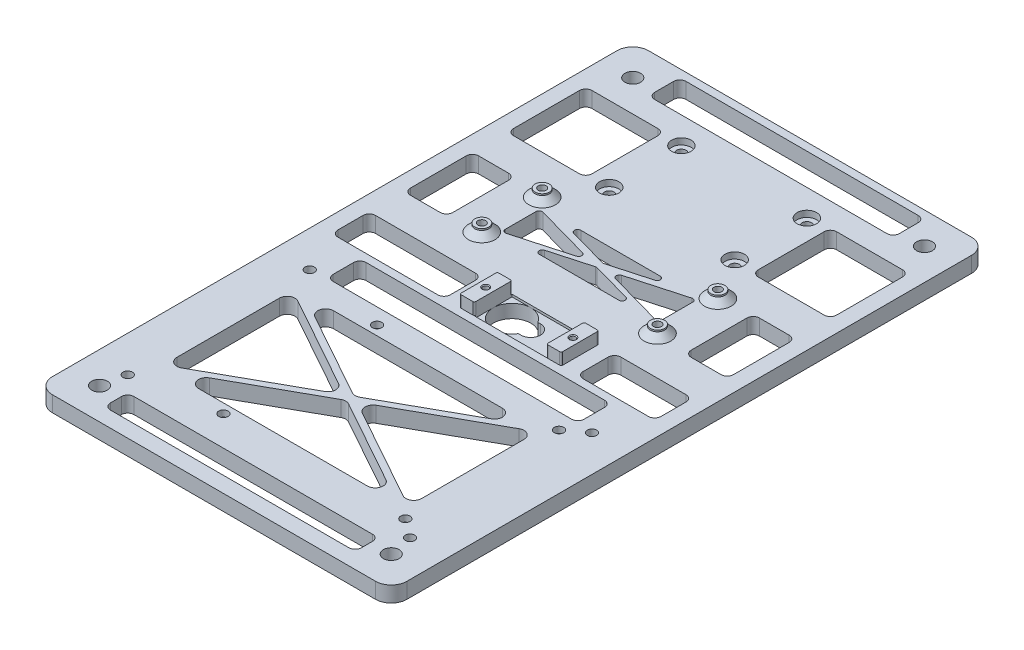
SolidWorks part; units mm, degrees
other "Markup1"
sketch "Sketch25" plane through (-56.5, 8.75, 95) normal (-0.8124, 0.5756, 0.0932) x (-0.5544, -0.812, 0.1827)
ref_plane "Front Plane" through (0, 0, 0) normal (0, 0, 1) x (1, 0, 0)
ref_plane "Top Plane" through (0, 0, 0) normal (0, 1, 0) x (1, 0, 0)
ref_plane "Right Plane" through (0, 0, 0) normal (1, 0, 0) x (0, 0, -1)
sketch "Sketch1" plane through (0, 0, 0) normal (0, 1, 0) x (1, 0, 0)
  line L0 (-56.5, -95) -> (-56.5, 95)
  line L1 (-46.5, -85) -> (46.5, -85) construction
  line L2 (-46.5, -85) -> (-46.5, 85) construction
  line L3 (-46.5, 85) -> (46.5, 85) construction
  line L4 (46.5, -85) -> (46.5, 85) construction
  line L5 (-46.5, -85) -> (46.5, 85) construction
  line L6 (-46.5, 85) -> (46.5, -85) construction
  line L7 (-56.5, 95) -> (56.5, 95)
  line L8 (56.5, -95) -> (56.5, 95)
  line L9 (-56.5, -95) -> (56.5, -95)
  circle A0 centre (46.5, 85) radius 2.5
  circle A1 centre (-46.5, 85) radius 2.5
  circle A2 centre (-46.5, -85) radius 2.5
  circle A3 centre (46.5, -85) radius 2.5
  point P0 (0, 0)
  dimension "D3" = 5
  dimension "D1" = 170
  dimension "D2" = 93
  dimension "D4" = 10
extrude "Boss-Extrude1" add sketch "Sketch1" along normal blind 5
fillet "Fillet1" radius 5 4 edges at (-56.5, 2.5, 95) (-56.5, 2.5, -95) (56.5, 2.5, -95) (56.5, 2.5, 95)
sketch "Sketch2" plane through (0, 5, 0) normal (0, 1, 0) x (1, 0, 0)
  line L0 (-39, -24) -> (-39, -73) construction
  line L1 (-39, -24) -> (39, -24) construction
  line L2 (-39, -20.5) -> (39, -20.5) construction
  line L3 (42.5, -48.5) -> (-39, -48.5) construction
  line L4 (-42.5, -24) -> (-42.5, -73) construction
  line L5 (42.5, -24) -> (42.5, -73) construction
  line L6 (-39, -76.5) -> (39, -76.5) construction
  line L7 (0, -20.5) -> (0, -1.8528) construction
  line L8 (-51.5, -95) -> (51.5, -95) construction
  circle A0 centre (39, -24) radius 1.5
  circle A1 centre (39, -73) radius 1.5
  arc A2 (-39, -20.5) -> (-42.5, -24) centre (-39, -24) ccw construction
  arc A3 (-39, -76.5) -> (-42.5, -73) centre (-39, -73) cw construction
  arc A4 (42.5, -24) -> (39, -20.5) centre (39, -24) ccw construction
  arc A5 (42.5, -73) -> (39, -76.5) centre (39, -73) cw construction
  circle A6 centre (-19, -24) radius 1.5
  circle A7 centre (-19, -73) radius 1.5
  point P14 (1.75, -48.5)
  dimension "D1" = 3
  dimension "D2" = 49
  dimension "D3" = 85
  dimension "D4" = 56
  dimension "D5" = 58
  dimension "D6" = 18.5
extrude "Cut-Extrude1" cut sketch "Sketch2" against normal blind 10
sketch "Sketch3" plane through (0, 5, 0) normal (0, 1, 0) x (1, 0, 0)
  line L0 (-45, -80) -> (45, -80) construction
  line L1 (-47.5, -77.5) -> (-47.5, -19.5) construction
  line L2 (-45, -17) -> (45, -17) construction
  line L3 (47.5, -77.5) -> (47.5, -19.5) construction
  line L4 (-47.5, -80) -> (47.5, -17) construction
  line L5 (-47.5, -17) -> (47.5, -80) construction
  line L6 (-51.5, -95) -> (51.5, -95) construction
  circle A0 centre (45, -19.5) radius 1.5
  circle A1 centre (45, -77.5) radius 1.5
  circle A2 centre (-45, -19.5) radius 1.5
  circle A3 centre (-45, -77.5) radius 1.5
  arc A4 (-47.5, -19.5) -> (-45, -17) centre (-45, -19.5) cw construction
  arc A5 (-45, -80) -> (-47.5, -77.5) centre (-45, -77.5) cw construction
  arc A6 (45, -80) -> (47.5, -77.5) centre (45, -77.5) ccw construction
  arc A7 (45, -17) -> (47.5, -19.5) centre (45, -19.5) cw construction
  point P0 (0, -48.5)
  dimension "D3" = 2.5
  dimension "D1" = 95
  dimension "D2" = 63
  dimension "D4" = 15
extrude "Cut-Extrude2" cut sketch "Sketch3" against normal blind 10
sketch "Sketch5" plane through (0, 5, 0) normal (0, 1, 0) x (1, 0, 0)
  line L1 (-38, -90) -> (38, -90)
  line L2 (-40, -88) -> (-40, -84.5)
  line L3 (-38, -82.5) -> (38, -82.5)
  line L4 (40, -88) -> (40, -84.5)
  line L5 (-40, -90) -> (40, -82.5) construction
  line L6 (-40, -82.5) -> (40, -90) construction
  circle A2 centre (-46.5, -85) radius 2.5 construction
  arc A3 (-38, -90) -> (-40, -88) centre (-38, -88) cw
  arc A4 (-40, -84.5) -> (-38, -82.5) centre (-38, -84.5) cw
  arc A5 (38, -82.5) -> (40, -84.5) centre (38, -84.5) cw
  arc A6 (38, -90) -> (40, -88) centre (38, -88) ccw
  point P0 (0, -86.25)
  dimension "D3" = 2
  dimension "D1" = 7.5
  dimension "D2" = 80
extrude "Cut-Extrude4" cut sketch "Sketch5" against normal blind 10
sketch "Sketch21" plane through (0, 5, 0) normal (0, 1, 0) x (1, 0, 0)
  line L4 (5.975, 2.875) -> (5.122, 2.875) construction
  line L5 (5.975, -2.875) -> (5.122, -2.875) construction
  line L6 (5.975, -3.125) -> (5.122, -3.125)
  line L7 (5.975, 3.125) -> (5.122, 3.125)
  arc A8 (4.9085, 2.9948) -> (4.9085, -2.9948) centre (0, 0) ccw construction
  arc A11 (5.975, -2.875) -> (5.975, 2.875) centre (5.975, 0) ccw construction
  arc A12 (4.9085, 2.9948) -> (5.122, 2.875) centre (5.122, 3.125) ccw construction
  arc A13 (5.122, -2.875) -> (4.9085, -2.9948) centre (5.122, -3.125) ccw construction
  arc A14 (5.122, 3.125) -> (5.122, -3.125) centre (0, 0) ccw
  arc A15 (5.122, -3.125) -> (5.122, -3.125) centre (5.122, -3.125) ccw
  arc A16 (5.975, -3.125) -> (5.975, 3.125) centre (5.975, 0) ccw
  arc A17 (5.122, 3.125) -> (5.122, 3.125) centre (5.122, 3.125) ccw
  dimension "D2" = 2.875
  dimension "D3" = 5.75
  dimension "D4" = 0.25
  dimension "D5" = 0.25
  dimension "D1" = 5.975
extrude "Cut-Extrude16" cut sketch "Sketch21" against normal through all
sketch "Sketch22" plane through (0, 5, 0) normal (0, 1, 0) x (1, 0, 0)
  line L0 (-6, 6) -> (-6, -6)
  line L1 (-6, 6) -> (17, 6)
  line L2 (-6, -6) -> (17, -6)
  line L3 (17, 6) -> (17, -6)
  arc A0 (5.122, 3.125) -> (5.122, -3.125) centre (0, 0) ccw construction
  dimension "D1" = 23
extrude "Cut-Extrude17" cut sketch "Sketch22" against normal blind 0.75
sketch "Sketch23" plane through (0, 5, 0) normal (0, 1, 0) x (1, 0, 0)
  line L0 (-6, 6) -> (-6, -6)
  line L1 (-6, 6) -> (-10.675, 6)
  line L2 (-6, -6) -> (-10.675, -6)
  line L3 (-10.675, 6) -> (-10.675, -6)
  line L4 (5.5, -6) -> (5.5, 6) construction
  line L5 (-6, -6) -> (17, -6) construction
  line L6 (17, 6) -> (-6, 6) construction
  line L7 (17, -6) -> (21.675, -6)
  line L8 (21.675, 6) -> (21.675, -6)
  line L9 (17, 6) -> (21.675, 6)
  line L10 (17, 6) -> (17, -6)
  circle A0 centre (-8.4, 0) radius 0.875
  circle A1 centre (19.4, 0) radius 0.875
  dimension "D2" = 1.75
  dimension "D1" = 4.675
  dimension "D3" = 2.4
extrude "Boss-Extrude5" add sketch "Sketch23" along normal blind 3.75
sketch "Sketch24" plane through (0, 5, 0) normal (0, 1, 0) x (1, 0, 0)
  circle A0 centre (19.4, 0) radius 0.875 construction
  circle A1 centre (-8.4, 0) radius 0.875 construction
  circle A2 centre (19.4, 0) radius 0.875
  circle A3 centre (-8.4, 0) radius 0.875
extrude "Cut-Extrude18" cut sketch "Sketch24" against normal blind 1.5
sketch "Sketch9" plane through (0, 5, 0) normal (0, 1, 0) x (1, 0, 0)
  line L0 (-48.1787, 10) -> (48.1787, 10)
  line L1 (-50, 11.8213) -> (-50, 38.1787)
  line L2 (-48.1787, 40) -> (48.1787, 40)
  line L3 (50, 11.8213) -> (50, 38.1787)
  line L4 (-50, 10) -> (50, 40) construction
  line L5 (-50, 40) -> (50, 10) construction
  arc A0 (48.1787, 40) -> (50, 38.1787) centre (48.1787, 38.1787) cw
  arc A1 (48.1787, 10) -> (50, 11.8213) centre (48.1787, 11.8213) ccw
  arc A2 (-48.1787, 10) -> (-50, 11.8213) centre (-48.1787, 11.8213) cw
  arc A3 (-50, 38.1787) -> (-48.1787, 40) centre (-48.1787, 38.1787) cw
  point P0 (0, 25)
  dimension "D4" = 1.8213
  dimension "D1" = 30
  dimension "D2" = 100
  dimension "D3" = 25
sketch "Sketch12" plane through (0, 5, 0) normal (0, 1, 0) x (1, 0, 0)
  line L1 (-51.5, 75) -> (-26.5, 75)
  line L2 (-51.5, 75) -> (-51.5, 50)
  line L3 (-51.5, 50) -> (-26.5, 50)
  line L4 (-26.5, 75) -> (-26.5, 50)
  line L6 (0, 0) -> (0, -22.2555) construction
  line L7 (26.5, 75) -> (26.5, 50)
  line L8 (51.5, 50) -> (26.5, 50)
  line L9 (51.5, 75) -> (51.5, 50)
  line L10 (51.5, 75) -> (26.5, 75)
  line L11 (-56.5, 90) -> (-56.5, -90) construction
  dimension "D1" = 25
  dimension "D2" = 25
  dimension "D3" = 50
  dimension "D4" = 5
extrude "Cut-Extrude9" cut sketch "Sketch12" against normal through all
sketch "Sketch15" plane through (0, 5, 0) normal (0, 1, 0) x (1, 0, 0)
  line L1 (-51.5, 6) -> (-15.675, 6)
  line L2 (-51.5, 6) -> (-51.5, -6)
  line L3 (-51.5, -6) -> (-15.675, -6)
  line L4 (-15.675, 6) -> (-15.675, -6)
  line L6 (-56.5, 90) -> (-56.5, -90) construction
  line L9 (26.675, 6) -> (51.5, 6)
  line L10 (26.675, 6) -> (26.675, -6)
  line L11 (26.675, -6) -> (51.5, -6)
  line L12 (51.5, 6) -> (51.5, -6)
  line L13 (56.5, -90) -> (56.5, 90) construction
  line L15 (17, 6) -> (-6, 6) construction
  line L16 (-6, -6) -> (17, -6) construction
  line L17 (21.675, -6) -> (21.675, 6) construction
  line L18 (-10.675, 6) -> (-10.675, -6) construction
  dimension "D1" = 5
  dimension "D2" = 5
  dimension "D3" = 5
  dimension "D4" = 5
extrude "Cut-Extrude11" cut sketch "Sketch15" against normal up to next
fillet "Fillet3" radius 2 16 edges at (-51.5, 2.5, 6) (-51.5, 2.5, -6) (-15.675, 2.5, -6) (-15.675, 2.5, 6) (51.5, 2.5, -6) (26.675, 2.5, -6) (26.675, 2.5, 6) (51.5, 2.5, 6) (51.5, 2.5, -50) (51.5, 2.5, -75) (26.5, 2.5, -50) (26.5, 2.5, -75) (-26.5, 2.5, -50) (-51.5, 2.5, -50) (-51.5, 2.5, -75) (-26.5, 2.5, -75)
sketch "Sketch16" plane through (0, 0, 0) normal (0, -1, 0) x (1, 0, 0)
  line L0 (-42, 64.8229) -> (-42, 32.1771)
  line L1 (-42.5, 70.5) -> (36.5, 70.5) construction
  line L2 (-42.5, 70.5) -> (-42.5, 26.5) construction
  line L3 (-42.5, 26.5) -> (36.5, 26.5) construction
  line L4 (36.5, 70.5) -> (36.5, 26.5) construction
  line L5 (-42.5, 70.5) -> (36.5, 26.5) construction
  line L6 (-42.5, 26.5) -> (36.5, 70.5) construction
  line L7 (-38.2835, 29.993) -> (-8.9766, 46.3159)
  line L8 (-8.9766, 50.6841) -> (-38.2835, 67.007)
  line L9 (-31.1371, 31.6841) -> (-4.2165, 46.6778)
  line L10 (-1.7835, 46.6778) -> (25.1371, 31.6841)
  line L11 (23.9206, 27) -> (-29.9206, 27)
  line L12 (-3, 48.5) -> (-3, 70.5) construction
  line L13 (-3, 48.5) -> (36.5, 48.5) construction
  line L14 (32.2835, 29.993) -> (2.9766, 46.3159)
  line L15 (36, 64.8229) -> (36, 32.1771)
  line L16 (2.9766, 50.6841) -> (32.2835, 67.007)
  line L17 (-1.7835, 50.3222) -> (25.1371, 65.3159)
  line L18 (-31.1371, 65.3159) -> (-4.2165, 50.3222)
  line L19 (23.9206, 70) -> (-29.9206, 70)
  line L20 (-33.5875, -28) -> (-33.5875, -6) construction
  line L26 (-28, -37.625) -> (28, -37.625) construction
  line L27 (-28, -37.625) -> (-28, -18.375) construction
  line L28 (-49.5, -6) -> (-17.675, -6) construction
  line L29 (-33.5875, -28) -> (-33.5875, -50) construction
  line L30 (51.5, -95) -> (-51.5, -95) construction
  line L31 (-37, -82.5) -> (37, -82.5)
  line L32 (-39, -84.5) -> (-39, -90.5)
  line L33 (-37, -92.5) -> (37, -92.5)
  line L34 (39, -84.5) -> (39, -90.5)
  line L35 (-39, -82.5) -> (39, -92.5) construction
  line L36 (-39, -92.5) -> (39, -82.5) construction
  line L37 (-28.5, -75) -> (-49.5, -75) construction
  line L44 (-49.5, -50) -> (-28.5, -50) construction
  line L63 (-28, -18.375) -> (28, -18.375) construction
  line L64 (28, -37.625) -> (28, -18.375) construction
  line L65 (-28, -37.625) -> (28, -18.375) construction
  line L66 (-28, -18.375) -> (28, -37.625) construction
  circle A0 centre (-45, 77.5) radius 1.5 construction
  circle A1 centre (39, 73) radius 1.5 construction
  circle A2 centre (39, 24) radius 1.5 construction
  circle A3 centre (-19, 73) radius 1.5 construction
  arc A4 (23.9206, 27) -> (25.1371, 31.6841) centre (23.9206, 29.5) ccw
  arc A5 (-1.7835, 46.6778) -> (-4.2165, 46.6778) centre (-3, 44.4938) ccw
  arc A6 (-29.9206, 27) -> (-31.1371, 31.6841) centre (-29.9206, 29.5) cw
  arc A7 (-42, 32.1771) -> (-38.2835, 29.993) centre (-39.5, 32.1771) ccw
  arc A8 (-8.9766, 46.3159) -> (-8.9766, 50.6841) centre (-10.193, 48.5) ccw
  arc A9 (-38.2835, 67.007) -> (-42, 64.8229) centre (-39.5, 64.8229) ccw
  arc A10 (36, 32.1771) -> (32.2835, 29.993) centre (33.5, 32.1771) cw
  arc A11 (2.9766, 46.3159) -> (2.9766, 50.6841) centre (4.193, 48.5) cw
  arc A12 (32.2835, 67.007) -> (36, 64.8229) centre (33.5, 64.8229) cw
  arc A13 (-1.7835, 50.3222) -> (-4.2165, 50.3222) centre (-3, 52.5062) cw
  arc A14 (23.9206, 70) -> (25.1371, 65.3159) centre (23.9206, 67.5) cw
  arc A15 (-29.9206, 70) -> (-31.1371, 65.3159) centre (-29.9206, 67.5) ccw
  circle A16 centre (-46.5, -85) radius 2.5 construction
  circle A17 centre (46.5, -85) radius 2.5 construction
  arc A30 (-39, -90.5) -> (-37, -92.5) centre (-37, -90.5) ccw
  arc A31 (37, -92.5) -> (39, -90.5) centre (37, -90.5) ccw
  arc A32 (39, -84.5) -> (37, -82.5) centre (37, -84.5) ccw
  arc A33 (-37, -82.5) -> (-39, -84.5) centre (-37, -84.5) ccw
  circle A34 centre (-28, -18.375) radius 1.25
  circle A35 centre (28, -18.375) radius 1.25
  circle A36 centre (28, -37.625) radius 1.25
  circle A37 centre (-28, -37.625) radius 1.25
  point P4 (-3, 48.5)
  point P52 (0, -28)
  point P69 (0, -87.5)
  dimension "D3" = 2.5
  dimension "D4" = 2.5
  dimension "D11" = 2.5
  dimension "D18" = 2
  dimension "D19" = 2
  dimension "D20" = 2.5
  dimension "D1" = 2.5
  dimension "D2" = 2.5
  dimension "D5" = 1
  dimension "D6" = 1
  dimension "D7" = 1
  dimension "D8" = 1
  dimension "D9" = 1
  dimension "D10" = 1
  dimension "D12" = 56
  dimension "D13" = 19.25
  dimension "D14" = 2.5
  dimension "D15" = 7.5
  dimension "D16" = 7.5
  dimension "D17" = 7.5
extrude "Cut-Extrude12" cut sketch "Sketch16" against normal up to next
sketch "Sketch17" plane through (0, 5, 0) normal (0, 1, 0) x (1, 0, 0)
  line L0 (0, 0) -> (0, 50000) construction
  line L1 (-40, 38.875) -> (-49.5, 38.875)
  line L2 (-38, 36.875) -> (-38, 19.125)
  line L3 (-40, 17.125) -> (-49.5, 17.125)
  line L4 (-51.5, 36.875) -> (-51.5, 19.125)
  line L5 (-38, 38.875) -> (-51.5, 17.125) construction
  line L6 (-38, 17.125) -> (-51.5, 38.875) construction
  line L7 (-51.5, 73) -> (-51.5, 52) construction
  line L8 (40, 17.125) -> (49.5, 17.125)
  line L9 (51.5, 36.875) -> (51.5, 19.125)
  line L10 (40, 38.875) -> (49.5, 38.875)
  line L11 (38, 36.875) -> (38, 19.125)
  circle A0 centre (-28, 18.375) radius 1.25 construction
  circle A1 centre (-28, 37.625) radius 1.25 construction
  arc A2 (-51.5, 19.125) -> (-49.5, 17.125) centre (-49.5, 19.125) ccw
  arc A3 (-40, 17.125) -> (-38, 19.125) centre (-40, 19.125) ccw
  arc A4 (-38, 36.875) -> (-40, 38.875) centre (-40, 36.875) ccw
  arc A5 (-49.5, 38.875) -> (-51.5, 36.875) centre (-49.5, 36.875) ccw
  arc A6 (51.5, 19.125) -> (49.5, 17.125) centre (49.5, 19.125) cw
  arc A7 (49.5, 38.875) -> (51.5, 36.875) centre (49.5, 36.875) cw
  arc A8 (40, 17.125) -> (38, 19.125) centre (40, 19.125) cw
  arc A9 (38, 36.875) -> (40, 38.875) centre (40, 36.875) cw
  point P4 (-44.75, 28)
  dimension "D2" = 2
  dimension "D1" = 10
extrude "Cut-Extrude13" cut sketch "Sketch17" against normal up to next
sketch "Sketch18" plane through (0, 5, 0) normal (0, 1, 0) x (1, 0, 0)
  line L0 (-25, 32.6293) -> (-25, 22.8516)
  line L1 (-25.5, 35.125) -> (25.5, 35.125) construction
  line L2 (-25.5, 35.125) -> (-25.5, 20.875) construction
  line L3 (-25.5, 20.875) -> (25.5, 20.875) construction
  line L4 (25.5, 35.125) -> (25.5, 20.875) construction
  line L5 (-25.5, 35.125) -> (25.5, 20.875) construction
  line L6 (-25.5, 20.875) -> (25.5, 35.125) construction
  line L7 (-23.7309, 21.8885) -> (-6.2339, 26.7773)
  line L8 (-6.2339, 28.7035) -> (-23.7309, 33.5924)
  line L9 (-12.6995, 34.625) -> (12.6995, 34.625)
  line L10 (12.9686, 32.6619) -> (0.2691, 29.1135)
  line L11 (-0.2691, 29.1135) -> (-12.9686, 32.6619)
  line L12 (0, 28) -> (0, 20.875) construction
  line L13 (0, 28) -> (25.5, 28) construction
  line L14 (23.7309, 21.8885) -> (6.2339, 26.7773)
  line L15 (25, 32.6293) -> (25, 22.8516)
  line L16 (6.2339, 28.7035) -> (23.7309, 33.5924)
  line L17 (12.9686, 23.3381) -> (0.2691, 26.8865)
  line L18 (-12.6995, 21.375) -> (12.6995, 21.375)
  line L19 (-0.2691, 26.8865) -> (-12.9686, 23.3381)
  line L20 (-49.5, -6) -> (-17.675, -6) construction
  line L21 (-38, -8.5) -> (38, -8.5)
  line L22 (-40, -10.5) -> (-40, -17)
  line L23 (-38, -19) -> (38, -19)
  line L24 (40, -10.5) -> (40, -17)
  line L25 (-40, -8.5) -> (40, -19) construction
  line L26 (-40, -19) -> (40, -8.5) construction
  circle A0 centre (-28, 37.625) radius 1.25 construction
  circle A1 centre (-28, 18.375) radius 1.25 construction
  circle A2 centre (28, 37.625) radius 1.25 construction
  arc A3 (-0.2691, 29.1135) -> (0.2691, 29.1135) centre (0, 30.0766) ccw
  arc A4 (12.9686, 32.6619) -> (12.6995, 34.625) centre (12.6995, 33.625) ccw
  arc A5 (-12.6995, 34.625) -> (-12.9686, 32.6619) centre (-12.6995, 33.625) ccw
  arc A6 (-25, 22.8516) -> (-23.7309, 21.8885) centre (-24, 22.8516) ccw
  arc A7 (-6.2339, 26.7773) -> (-6.2339, 28.7035) centre (-6.503, 27.7404) ccw
  arc A8 (-23.7309, 33.5924) -> (-25, 32.6293) centre (-24, 32.6293) ccw
  arc A9 (25, 22.8516) -> (23.7309, 21.8885) centre (24, 22.8516) cw
  arc A10 (6.2339, 26.7773) -> (6.2339, 28.7035) centre (6.503, 27.7404) cw
  arc A11 (23.7309, 33.5924) -> (25, 32.6293) centre (24, 32.6293) cw
  arc A12 (12.9686, 23.3381) -> (12.6995, 21.375) centre (12.6995, 22.375) cw
  arc A13 (-0.2691, 26.8865) -> (0.2691, 26.8865) centre (0, 25.9234) cw
  arc A14 (-12.6995, 21.375) -> (-12.9686, 23.3381) centre (-12.6995, 22.375) cw
  circle A15 centre (-45, -19.5) radius 1.5 construction
  circle A16 centre (45, -19.5) radius 1.5 construction
  circle A17 centre (39, -24) radius 1.5 construction
  arc A18 (38, -8.5) -> (40, -10.5) centre (38, -10.5) cw
  arc A19 (40, -17) -> (38, -19) centre (38, -17) cw
  arc A20 (-38, -19) -> (-40, -17) centre (-38, -17) cw
  arc A21 (-38, -8.5) -> (-40, -10.5) centre (-38, -10.5) ccw
  point P4 (0, 28)
  point P54 (0, -13.75)
  dimension "D11" = 1
  dimension "D13" = 5
  dimension "D16" = 2
  dimension "D1" = 2.5
  dimension "D2" = 2.5
  dimension "D3" = 2.5
  dimension "D4" = 2.5
  dimension "D5" = 1
  dimension "D6" = 1
  dimension "D7" = 1
  dimension "D8" = 1
  dimension "D9" = 1
  dimension "D10" = 1
  dimension "D12" = 5
  dimension "D14" = 5
  dimension "D15" = 2.5
extrude "Cut-Extrude14" cut sketch "Sketch18" against normal through all
sketch "Sketch19" plane through (0, 5, 0) normal (0, 1, 0) x (1, 0, 0)
  circle A0 centre (-28, 18.375) radius 1.25 construction
  circle A1 centre (28, 18.375) radius 1.25 construction
  circle A2 centre (28, 37.625) radius 1.25 construction
  circle A3 centre (-28, 37.625) radius 1.25 construction
  circle A4 centre (-28, 18.375) radius 1.25
  circle A5 centre (28, 18.375) radius 1.25
  circle A6 centre (28, 37.625) radius 1.25
  circle A7 centre (-28, 37.625) radius 1.25
  circle A8 centre (-28, 37.625) radius 2.25
  circle A9 centre (-28, 18.375) radius 2.25
  circle A10 centre (28, 37.625) radius 2.25
  circle A11 centre (28, 18.375) radius 2.25
  dimension "D1" = 1
  dimension "D2" = 1
  dimension "D3" = 1
  dimension "D4" = 1
extrude "Boss-Extrude4" add sketch "Sketch19" along normal blind 2.5
chamfer "Chamfer1" distance 2 angle 45 4 edges at (-28, 5, -35.375) (-28, 5, -16.125) (28, 5, -16.125) (28, 5, -35.375)
sketch "Sketch20" plane through (0, 0, 0) normal (0, -1, 0) x (1, 0, 0)
  circle A0 centre (-19, 73) radius 2.5
  circle A1 centre (-19, 24) radius 2.5
  circle A2 centre (39, 24) radius 2.5
  circle A4 centre (39, 73) radius 2.5
  dimension "D1" = 5
extrude "Cut-Extrude15" cut sketch "Sketch20" against normal blind 3
fillet "Fillet4" radius 0.5 8 edges at (21.675, 6.875, -6) (17, 6.875, -6) (-10.675, 6.875, -6) (-6, 6.875, -6) (17, 6.875, 6) (-6, 6.875, 6) (21.675, 6.875, 6) (-10.675, 6.875, 6)
chamfer "Chamfer2" distance 0.25 angle 45 2 edges at (-8.4, 8.75, 0.875) (19.4, 8.75, -0.875)
sketch "Sketch26" plane through (0, 5, 0) normal (0, 1, 0) x (1, 0, 0)
  line L0 (-26.5, 52) -> (-26.5, 73) construction
  line L1 (-20, 51) -> (20, 51) construction
  line L2 (-20, 51) -> (-20, 74) construction
  line L3 (-20, 74) -> (20, 74) construction
  line L4 (20, 51) -> (20, 74) construction
  line L5 (-20, 51) -> (20, 74) construction
  line L6 (-20, 74) -> (20, 51) construction
  circle A0 centre (-20, 74) radius 1.5
  circle A1 centre (-20, 51) radius 1.5
  circle A2 centre (20, 74) radius 1.5
  circle A3 centre (20, 51) radius 1.5
  point P0 (0, 62.5)
  point P11 (-26.5, 62.5)
  dimension "D3" = 3
  dimension "D1" = 40
  dimension "D2" = 23
extrude "Cut-Extrude19" cut sketch "Sketch26" against normal through all
sketch "Sketch27" plane through (0, 5, 0) normal (0, 1, 0) x (1, 0, 0)
  circle A0 centre (-20, 74) radius 3.1
  circle A1 centre (-20, 51) radius 3.1
  circle A2 centre (20, 51) radius 3.1
  circle A3 centre (20, 74) radius 3.1
  dimension "D1" = 6.2
extrude "Cut-Extrude20" cut sketch "Sketch27" against normal blind 2
